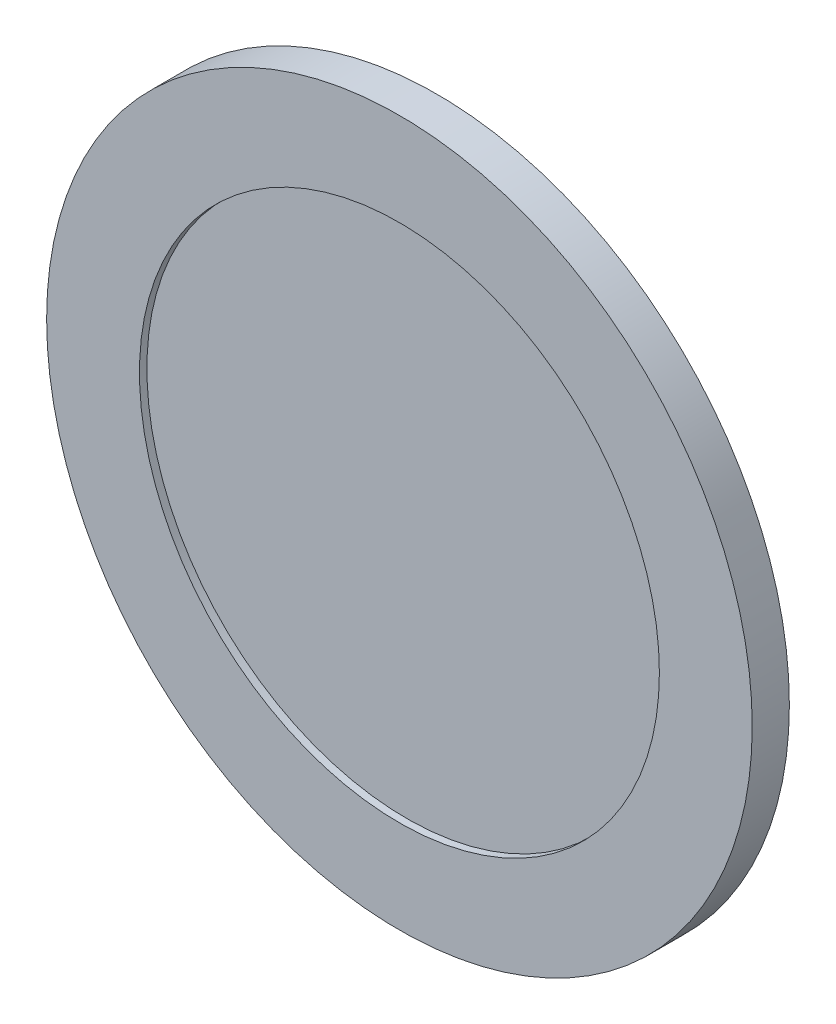
SolidWorks part; units mm, degrees
ref_plane "Front Plane" through (0, 0, 0) normal (0, 0, 1) x (1, 0, 0)
ref_plane "Top Plane" through (0, 0, 0) normal (0, 1, 0) x (1, 0, 0)
ref_plane "Right Plane" through (0, 0, 0) normal (1, 0, 0) x (0, 0, -1)
sketch "Sketch1" plane through (0, 0, 0) normal (0, 0, 1) x (1, 0, 0)
  line L0 (0, 0) -> (0, -24.5788) construction
  circle A0 centre (0, 0) radius 9.5
  dimension "D1" = 19
extrude "Boss-Extrude1" add sketch "Sketch1" along normal blind 1
sketch "Sketch2" plane through (0, 0, 1) normal (0, 0, 1) x (1, 0, 0)
  circle A0 centre (0, 0) radius 7
  dimension "D1" = 14
extrude "Cut-Extrude1" cut sketch "Sketch2" against normal blind 0.2
